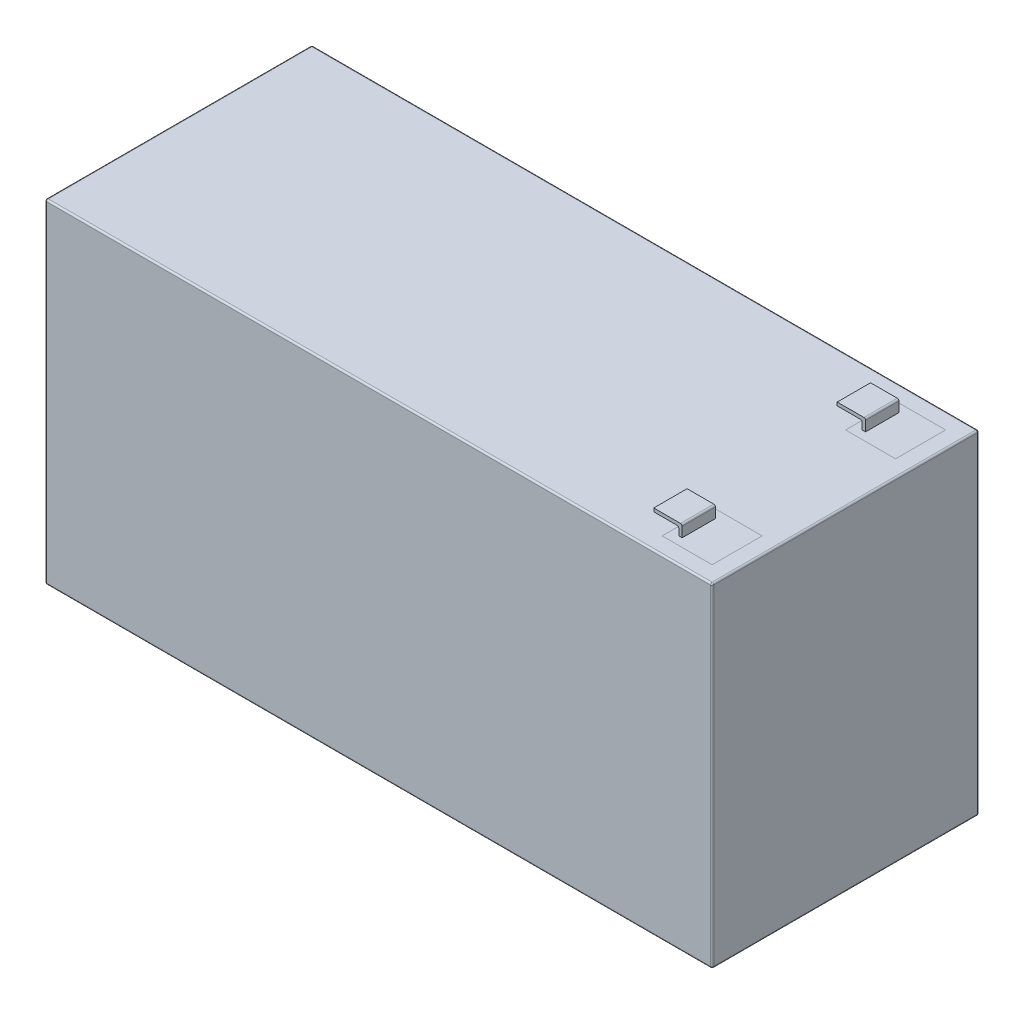
SolidWorks part; units mm, degrees
ref_plane "Front Plane" through (0, 0, 0) normal (0, 0, 1) x (1, 0, 0)
ref_plane "Top Plane" through (0, 0, 0) normal (0, 1, 0) x (1, 0, 0)
ref_plane "Right Plane" through (0, 0, 0) normal (1, 0, 0) x (0, 0, -1)
sketch "Sketch1" plane through (0, 0, 0) normal (0, 1, 0) x (1, 0, 0)
  line L1 (-50.8, -20.32) -> (50.8, -20.32)
  line L2 (-50.8, -20.32) -> (-50.8, 20.32)
  line L3 (-50.8, 20.32) -> (50.8, 20.32)
  line L4 (50.8, -20.32) -> (50.8, 20.32)
  line L5 (-50.8, -20.32) -> (50.8, 20.32) construction
  line L6 (-50.8, 20.32) -> (50.8, -20.32) construction
  point P0 (0, 0)
  dimension "D1" = 40.64
  dimension "D2" = 101.6
extrude "Boss-Extrude1" add sketch "Sketch1" along normal blind 50.8
sketch "Sketch2" plane through (0, 50.8, 0) normal (0, 1, 0) x (1, 0, 0)
  line L0 (0, 0) -> (50.8, 0) construction
  line L1 (40.64, 17.78) -> (48.26, 17.78)
  line L2 (40.64, 17.78) -> (40.64, 10.16)
  line L3 (40.64, 10.16) -> (48.26, 10.16)
  line L4 (48.26, 17.78) -> (48.26, 10.16)
  line L5 (50.8, -20.32) -> (50.8, 20.32) construction
  line L6 (48.26, -17.78) -> (48.26, -10.16)
  line L7 (40.64, -10.16) -> (48.26, -10.16)
  line L8 (40.64, -17.78) -> (40.64, -10.16)
  line L9 (40.64, -17.78) -> (48.26, -17.78)
  line L10 (50.8, 20.32) -> (-50.8, 20.32) construction
  dimension "D1" = 2.54
  dimension "D2" = 2.54
  dimension "D3" = 7.62
  dimension "D4" = 7.62
split line "Split Line1"
sketch "Sketch3" plane through (0, 0, -20.32) normal (0, 0, -1) x (-1, 0, 0)
  line L0 (-42.418, 50.8) -> (-42.418, 52.578)
  line L1 (-50.8, 50.8) -> (50.8, 50.8) construction
  line L2 (-42.418, 52.578) -> (-38.0987, 52.578)
  line L3 (-38.0987, 52.578) -> (-38.0987, 52.07)
  line L4 (-38.0987, 52.07) -> (-41.91, 52.07)
  line L5 (-41.91, 52.07) -> (-41.91, 50.8)
  line L6 (-42.418, 50.8) -> (-41.91, 50.8)
  point P4 (-38.1665, 51.8933)
  dimension "D1" = 0.508
  dimension "D2" = 3.8113
  dimension "D3" = 1.27
  dimension "D4" = 1.27
extrude "Boss-Extrude2" add sketch "Sketch3" along normal blind 5.08 from offset 8.89 offset against normal yes
mirror "Mirror1" about plane through (0, 0, 0) normal (0, 0, 1) of "Boss-Extrude2"
fillet "Fillet1" radius 0.254 16 edges at (42.418, 52.578, -13.97) (41.91, 52.07, -13.97) (41.91, 52.07, 13.97) (42.418, 52.578, 13.97) (-50.8, 0, 0) (-50.8, 25.4, 20.32) (0, 0, 20.32) (50.8, 25.4, 20.32) (50.8, 0, 0) (50.8, 25.4, -20.32) (-50.8, 25.4, -20.32) (0, 0, -20.32) (0, 50.8, 20.32) (-50.8, 50.8, 0) (0, 50.8, -20.32) (50.8, 50.8, 0)
